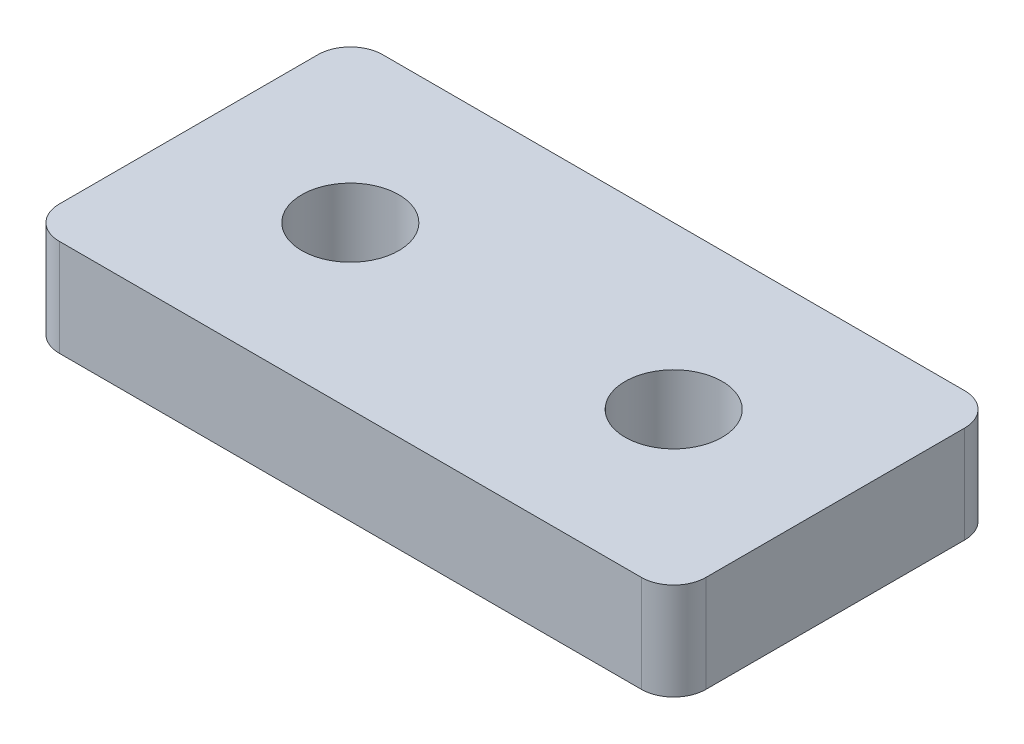
SolidWorks part; units mm, degrees
ref_plane "Front Plane" through (0, 0, 0) normal (0, 0, 1) x (1, 0, 0)
ref_plane "Top Plane" through (0, 0, 0) normal (0, 1, 0) x (1, 0, 0)
ref_plane "Right Plane" through (0, 0, 0) normal (1, 0, 0) x (0, 0, -1)
sketch "Sketch1" plane through (0, 0, 0) normal (0, 1, 0) x (1, 0, 0)
  line L1 (0, 0) -> (20, 0)
  line L2 (0, 0) -> (0, 10)
  line L3 (0, 10) -> (20, 10)
  line L4 (20, 0) -> (20, 10)
  circle A0 centre (5, 5) radius 1.5
  circle A1 centre (15, 5) radius 1.5
  dimension "D3" = 3
  dimension "D4" = 3
  dimension "D1" = 20
  dimension "D2" = 10
  dimension "D5" = 5
  dimension "D6" = 5
  dimension "D7" = 5
  dimension "D8" = 5
extrude "Boss-Extrude1" add sketch "Sketch1" along normal blind 3
fillet "Fillet1" radius 1 4 edges at (0, 1.5, -10) (0, 1.5, 0) (20, 1.5, -10) (20, 1.5, 0)
